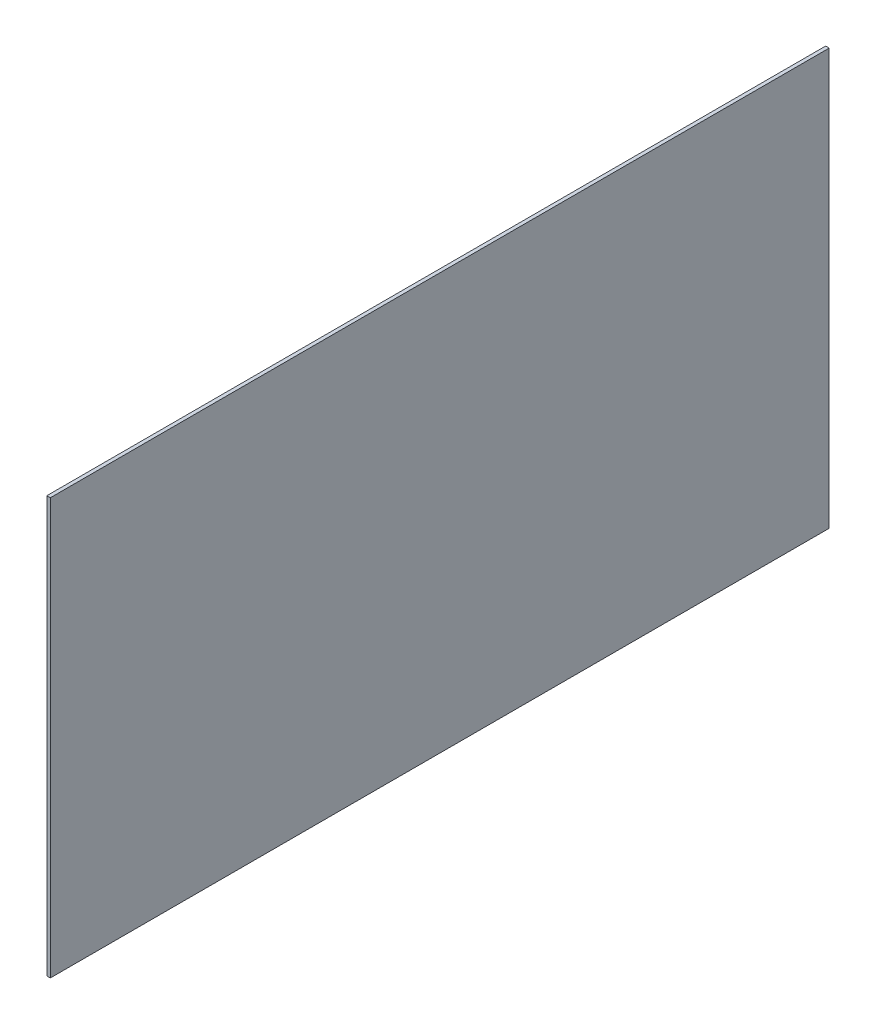
SolidWorks part; units mm, degrees
ref_plane "Front Plane" through (0, 0, 0) normal (0, 0, 1) x (1, 0, 0)
ref_plane "Top Plane" through (0, 0, 0) normal (0, 1, 0) x (1, 0, 0)
ref_plane "Right Plane" through (0, 0, 0) normal (1, 0, 0) x (0, 0, -1)
sketch "Sketch1" plane through (0, 0, 0) normal (0, 0, 1) x (1, 0, 0)
  line L0 (-418.175, 992.1) -> (-418.175, 1168.4)
  line L1 (-418.175, 1168.4) -> (-544.425, 1168.4) construction
  line L2 (-545.175, 1168.4) -> (-543.675, 1168.4) construction
extrude "Extrude-Thin1" add sketch "Sketch1" along normal mid plane 330.2 thin thin type mid plane wall 1.5
